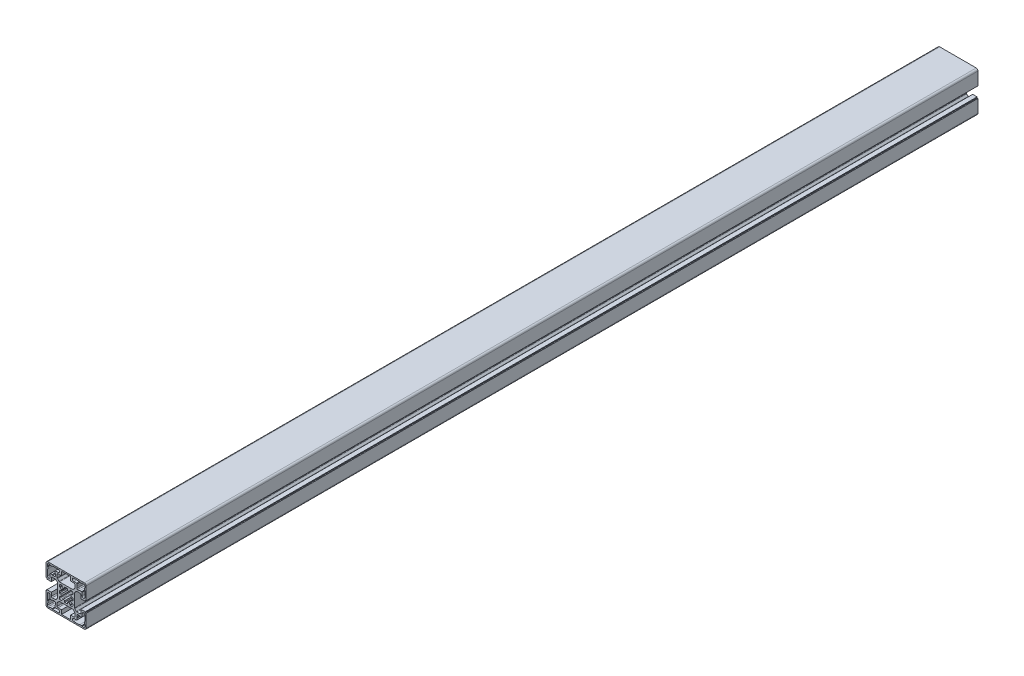
SolidWorks part; units mm, degrees
ref_plane "前视基准面" through (0, 0, 0) normal (0, 0, 1) x (1, 0, 0)
ref_plane "上视基准面" through (0, 0, 0) normal (0, 1, 0) x (1, 0, 0)
ref_plane "右视基准面" through (0, 0, 0) normal (1, 0, 0) x (0, 0, -1)
sketch "草图1" plane through (0, 0, 0) normal (0, 0, 1) x (1, 0, 0)
  line L8 (30.535, 44.0271) -> (29.0823, 45.4798)
  line L9 (31.4137, 44.0271) -> (30.535, 44.0271)
  line L10 (31.4137, 42.0271) -> (31.4137, 44.0271)
  line L11 (28.4137, 41.0271) -> (30.4137, 41.0271)
  line L12 (28.4137, 41.9058) -> (28.4137, 41.0271)
  line L13 (26.961, 43.3585) -> (28.4137, 41.9058)
  line L14 (25.4137, 41.0271) -> (25.4137, 42.7176)
  line L15 (22.4137, 41.0271) -> (25.4137, 41.0271)
  line L16 (22.4137, 42.7176) -> (22.4137, 41.0271)
  line L17 (19.4137, 41.9058) -> (20.8664, 43.3585)
  line L18 (19.4137, 41.0271) -> (19.4137, 41.9058)
  line L19 (17.4137, 41.0271) -> (19.4137, 41.0271)
  line L20 (16.4137, 44.0271) -> (16.4137, 42.0271)
  line L21 (17.2924, 44.0271) -> (16.4137, 44.0271)
  line L22 (18.7451, 45.4798) -> (17.2924, 44.0271)
  line L23 (16.4137, 47.0271) -> (18.1042, 47.0271)
  line L24 (16.4137, 50.0271) -> (16.4137, 47.0271)
  line L25 (18.1042, 50.0271) -> (16.4137, 50.0271)
  line L26 (17.2924, 53.0271) -> (18.7451, 51.5744)
  line L27 (16.4137, 53.0271) -> (17.2924, 53.0271)
  line L28 (16.4137, 55.0271) -> (16.4137, 53.0271)
  line L29 (19.4137, 56.0271) -> (17.4137, 56.0271)
  line L30 (19.4137, 55.1484) -> (19.4137, 56.0271)
  line L31 (20.8664, 53.6957) -> (19.4137, 55.1484)
  line L32 (22.4137, 56.0271) -> (22.4137, 54.3366)
  line L33 (25.4137, 56.0271) -> (22.4137, 56.0271)
  line L34 (25.4137, 54.3366) -> (25.4137, 56.0271)
  line L35 (28.4137, 55.1484) -> (26.961, 53.6957)
  line L36 (28.4137, 56.0271) -> (28.4137, 55.1484)
  line L37 (30.4137, 56.0271) -> (28.4137, 56.0271)
  line L38 (31.4137, 53.0271) -> (31.4137, 55.0271)
  line L39 (30.535, 53.0271) -> (31.4137, 53.0271)
  line L40 (29.0823, 51.5744) -> (30.535, 53.0271)
  line L41 (31.4137, 50.0271) -> (29.7232, 50.0271)
  line L42 (31.4137, 47.0271) -> (31.4137, 50.0271)
  line L43 (29.7232, 47.0271) -> (31.4137, 47.0271)
  line L44 (11.4137, 66.0271) -> (11.9137, 66.5271)
  line L45 (11.4137, 64.0271) -> (11.4137, 66.0271)
  line L46 (11.9137, 63.5271) -> (11.4137, 64.0271)
  line L47 (11.9137, 61.5271) -> (11.9137, 63.5271)
  line L48 (8.9137, 60.5271) -> (10.9137, 60.5271)
  line L49 (8.4137, 61.0271) -> (8.9137, 60.5271)
  line L50 (6.4137, 61.0271) -> (8.4137, 61.0271)
  line L51 (5.9137, 60.5271) -> (6.4137, 61.0271)
  line L52 (5.9137, 57.1271) -> (5.9137, 60.5271)
  line L53 (2.9137, 63.5271) -> (2.9137, 57.1271)
  line L54 (3.4137, 64.0271) -> (2.9137, 63.5271)
  line L55 (3.4137, 66.0271) -> (3.4137, 64.0271)
  line L56 (2.9137, 66.5271) -> (3.4137, 66.0271)
  line L57 (2.9137, 68.5271) -> (2.9137, 66.5271)
  line L58 (5.9137, 69.5271) -> (3.9137, 69.5271)
  line L59 (6.4137, 69.0271) -> (5.9137, 69.5271)
  line L60 (8.4137, 69.0271) -> (6.4137, 69.0271)
  line L61 (8.9137, 69.5271) -> (8.4137, 69.0271)
  line L62 (15.3137, 69.5271) -> (8.9137, 69.5271)
  line L63 (11.9137, 66.5271) -> (15.3137, 66.5271)
  line L64 (15.3137, 30.5271) -> (11.9137, 30.5271)
  line L65 (8.9137, 27.5271) -> (15.3137, 27.5271)
  line L66 (8.4137, 28.0271) -> (8.9137, 27.5271)
  line L67 (6.4137, 28.0271) -> (8.4137, 28.0271)
  line L68 (5.9137, 27.5271) -> (6.4137, 28.0271)
  line L69 (3.9137, 27.5271) -> (5.9137, 27.5271)
  line L70 (2.9137, 30.5271) -> (2.9137, 28.5271)
  line L71 (3.4137, 31.0271) -> (2.9137, 30.5271)
  line L72 (3.4137, 33.0271) -> (3.4137, 31.0271)
  line L73 (2.9137, 33.5271) -> (3.4137, 33.0271)
  line L74 (2.9137, 39.9271) -> (2.9137, 33.5271)
  line L75 (5.9137, 36.5271) -> (5.9137, 39.9271)
  line L76 (6.4137, 36.0271) -> (5.9137, 36.5271)
  line L77 (8.4137, 36.0271) -> (6.4137, 36.0271)
  line L78 (8.9137, 36.5271) -> (8.4137, 36.0271)
  line L79 (10.9137, 36.5271) -> (8.9137, 36.5271)
  line L80 (11.9137, 33.5271) -> (11.9137, 35.5271)
  line L81 (11.4137, 33.0271) -> (11.9137, 33.5271)
  line L82 (11.4137, 31.0271) -> (11.4137, 33.0271)
  line L83 (11.9137, 30.5271) -> (11.4137, 31.0271)
  line L84 (41.9137, 39.9271) -> (41.9137, 36.5271)
  line L85 (44.9137, 33.5271) -> (44.9137, 39.9271)
  line L86 (44.4137, 33.0271) -> (44.9137, 33.5271)
  line L87 (44.4137, 31.0271) -> (44.4137, 33.0271)
  line L88 (44.9137, 30.5271) -> (44.4137, 31.0271)
  line L89 (44.9137, 28.5271) -> (44.9137, 30.5271)
  line L90 (41.9137, 27.5271) -> (43.9137, 27.5271)
  line L91 (41.4137, 28.0271) -> (41.9137, 27.5271)
  line L92 (39.4137, 28.0271) -> (41.4137, 28.0271)
  line L93 (38.9137, 27.5271) -> (39.4137, 28.0271)
  line L94 (32.5137, 27.5271) -> (38.9137, 27.5271)
  line L95 (35.9137, 30.5271) -> (32.5137, 30.5271)
  line L96 (36.4137, 31.0271) -> (35.9137, 30.5271)
  line L97 (36.4137, 33.0271) -> (36.4137, 31.0271)
  line L98 (35.9137, 33.5271) -> (36.4137, 33.0271)
  line L99 (35.9137, 35.5271) -> (35.9137, 33.5271)
  line L100 (38.9137, 36.5271) -> (36.9137, 36.5271)
  line L101 (39.4137, 36.0271) -> (38.9137, 36.5271)
  line L102 (41.4137, 36.0271) -> (39.4137, 36.0271)
  line L103 (41.9137, 36.5271) -> (41.4137, 36.0271)
  line L104 (32.5137, 66.5271) -> (35.9137, 66.5271)
  line L105 (38.9137, 69.5271) -> (32.5137, 69.5271)
  line L106 (39.4137, 69.0271) -> (38.9137, 69.5271)
  line L107 (41.4137, 69.0271) -> (39.4137, 69.0271)
  line L108 (41.9137, 69.5271) -> (41.4137, 69.0271)
  line L109 (43.9137, 69.5271) -> (41.9137, 69.5271)
  line L110 (44.9137, 66.5271) -> (44.9137, 68.5271)
  line L111 (44.4137, 66.0271) -> (44.9137, 66.5271)
  line L112 (44.4137, 64.0271) -> (44.4137, 66.0271)
  line L113 (44.9137, 63.5271) -> (44.4137, 64.0271)
  line L114 (44.9137, 57.1271) -> (44.9137, 63.5271)
  line L115 (41.9137, 60.5271) -> (41.9137, 57.1271)
  line L116 (41.4137, 61.0271) -> (41.9137, 60.5271)
  line L117 (39.4137, 61.0271) -> (41.4137, 61.0271)
  line L118 (38.9137, 60.5271) -> (39.4137, 61.0271)
  line L119 (36.9137, 60.5271) -> (38.9137, 60.5271)
  line L120 (35.9137, 63.5271) -> (35.9137, 61.5271)
  line L121 (36.4137, 64.0271) -> (35.9137, 63.5271)
  line L122 (36.4137, 66.0271) -> (36.4137, 64.0271)
  line L123 (35.9137, 66.5271) -> (36.4137, 66.0271)
  line L124 (29.0137, 69.5271) -> (18.8137, 69.5271)
  line L125 (29.0137, 65.0271) -> (29.0137, 69.5271)
  line L126 (32.9137, 65.0271) -> (29.0137, 65.0271)
  line L127 (33.9137, 60.7091) -> (33.9137, 64.0271)
  line L128 (31.9388, 58.32) -> (33.6208, 60.002)
  line L129 (16.5957, 58.0271) -> (31.2317, 58.0271)
  line L130 (14.2066, 60.002) -> (15.8886, 58.32)
  line L131 (13.9137, 64.0271) -> (13.9137, 60.7091)
  line L132 (18.8137, 65.0271) -> (14.9137, 65.0271)
  line L133 (18.8137, 69.5271) -> (18.8137, 65.0271)
  line L134 (29.0137, 32.0271) -> (32.9137, 32.0271)
  line L135 (29.0137, 27.5271) -> (29.0137, 32.0271)
  line L136 (18.8137, 27.5271) -> (29.0137, 27.5271)
  line L137 (18.8137, 32.0271) -> (18.8137, 27.5271)
  line L138 (14.9137, 32.0271) -> (18.8137, 32.0271)
  line L139 (13.9137, 36.3451) -> (13.9137, 33.0271)
  line L140 (15.8886, 38.7342) -> (14.2066, 37.0522)
  line L141 (31.2317, 39.0271) -> (16.5957, 39.0271)
  line L142 (33.6208, 37.0522) -> (31.9388, 38.7342)
  line L143 (33.9137, 33.0271) -> (33.9137, 36.3451)
  line L144 (46.4137, 42.4271) -> (46.4137, 28.0271)
  line L145 (45.4137, 42.4271) -> (46.4137, 42.4271)
  line L146 (45.4137, 43.4271) -> (45.4137, 42.4271)
  line L147 (40.4137, 43.4271) -> (45.4137, 43.4271)
  line L148 (40.4137, 39.5271) -> (40.4137, 43.4271)
  line L149 (36.0957, 38.5271) -> (39.4137, 38.5271)
  line L150 (33.7066, 40.502) -> (35.3886, 38.82)
  line L151 (33.4137, 55.8451) -> (33.4137, 41.2091)
  line L152 (35.3886, 58.2342) -> (33.7066, 56.5522)
  line L153 (39.4137, 58.5271) -> (36.0957, 58.5271)
  line L154 (40.4137, 53.6271) -> (40.4137, 57.5271)
  line L155 (45.4137, 53.6271) -> (40.4137, 53.6271)
  line L156 (45.4137, 54.6271) -> (45.4137, 53.6271)
  line L157 (46.4137, 54.6271) -> (45.4137, 54.6271)
  line L158 (46.4137, 69.0271) -> (46.4137, 54.6271)
  line L159 (3.4137, 71.0271) -> (44.4137, 71.0271)
  line L160 (1.4137, 54.6271) -> (1.4137, 69.0271)
  line L161 (2.4137, 54.6271) -> (1.4137, 54.6271)
  line L162 (2.4137, 53.6271) -> (2.4137, 54.6271)
  line L163 (7.4137, 53.6271) -> (2.4137, 53.6271)
  line L164 (7.4137, 57.5271) -> (7.4137, 53.6271)
  line L165 (11.7317, 58.5271) -> (8.4137, 58.5271)
  line L166 (14.1208, 56.5522) -> (12.4388, 58.2342)
  line L167 (14.4137, 41.2091) -> (14.4137, 55.8451)
  line L168 (12.4388, 38.82) -> (14.1208, 40.502)
  line L169 (8.4137, 38.5271) -> (11.7317, 38.5271)
  line L170 (7.4137, 43.4271) -> (7.4137, 39.5271)
  line L171 (2.4137, 43.4271) -> (7.4137, 43.4271)
  line L172 (2.4137, 42.4271) -> (2.4137, 43.4271)
  line L173 (1.4137, 42.4271) -> (2.4137, 42.4271)
  line L174 (1.4137, 28.0271) -> (1.4137, 42.4271)
  line L175 (44.4137, 26.0271) -> (3.4137, 26.0271)
  arc A0 (30.4137, 41.0271) -> (31.4137, 42.0271) centre (30.4137, 42.0271) ccw
  arc A1 (25.4137, 42.7176) -> (26.961, 43.3585) centre (23.9137, 48.5271) ccw
  arc A2 (20.8664, 43.3585) -> (22.4137, 42.7176) centre (23.9137, 48.5271) ccw
  arc A3 (16.4137, 42.0271) -> (17.4137, 41.0271) centre (17.4137, 42.0271) ccw
  arc A4 (18.1042, 47.0271) -> (18.7451, 45.4798) centre (23.9137, 48.5271) ccw
  arc A5 (18.7451, 51.5744) -> (18.1042, 50.0271) centre (23.9137, 48.5271) ccw
  arc A6 (17.4137, 56.0271) -> (16.4137, 55.0271) centre (17.4137, 55.0271) ccw
  arc A7 (22.4137, 54.3366) -> (20.8664, 53.6957) centre (23.9137, 48.5271) ccw
  arc A8 (26.961, 53.6957) -> (25.4137, 54.3366) centre (23.9137, 48.5271) ccw
  arc A9 (31.4137, 55.0271) -> (30.4137, 56.0271) centre (30.4137, 55.0271) ccw
  arc A10 (29.7232, 50.0271) -> (29.0823, 51.5744) centre (23.9137, 48.5271) ccw
  arc A11 (29.0823, 45.4798) -> (29.7232, 47.0271) centre (23.9137, 48.5271) ccw
  arc A12 (10.9137, 60.5271) -> (11.9137, 61.5271) centre (10.9137, 61.5271) ccw
  arc A13 (2.9137, 57.1271) -> (5.9137, 57.1271) centre (4.4137, 57.1271) ccw
  arc A14 (3.9137, 69.5271) -> (2.9137, 68.5271) centre (3.9137, 68.5271) ccw
  arc A15 (15.3137, 66.5271) -> (15.3137, 69.5271) centre (15.3137, 68.0271) ccw
  arc A16 (15.3137, 27.5271) -> (15.3137, 30.5271) centre (15.3137, 29.0271) ccw
  arc A17 (2.9137, 28.5271) -> (3.9137, 27.5271) centre (3.9137, 28.5271) ccw
  arc A18 (5.9137, 39.9271) -> (2.9137, 39.9271) centre (4.4137, 39.9271) ccw
  arc A19 (11.9137, 35.5271) -> (10.9137, 36.5271) centre (10.9137, 35.5271) ccw
  arc A20 (44.9137, 39.9271) -> (41.9137, 39.9271) centre (43.4137, 39.9271) ccw
  arc A21 (43.9137, 27.5271) -> (44.9137, 28.5271) centre (43.9137, 28.5271) ccw
  arc A22 (32.5137, 30.5271) -> (32.5137, 27.5271) centre (32.5137, 29.0271) ccw
  arc A23 (36.9137, 36.5271) -> (35.9137, 35.5271) centre (36.9137, 35.5271) ccw
  arc A24 (32.5137, 69.5271) -> (32.5137, 66.5271) centre (32.5137, 68.0271) ccw
  arc A25 (44.9137, 68.5271) -> (43.9137, 69.5271) centre (43.9137, 68.5271) ccw
  arc A26 (41.9137, 57.1271) -> (44.9137, 57.1271) centre (43.4137, 57.1271) ccw
  arc A27 (35.9137, 61.5271) -> (36.9137, 60.5271) centre (36.9137, 61.5271) ccw
  arc A28 (33.9137, 64.0271) -> (32.9137, 65.0271) centre (32.9137, 64.0271) ccw
  arc A29 (33.6208, 60.002) -> (33.9137, 60.7091) centre (32.9137, 60.7091) ccw
  arc A30 (31.2317, 58.0271) -> (31.9388, 58.32) centre (31.2317, 59.0271) ccw
  arc A31 (15.8886, 58.32) -> (16.5957, 58.0271) centre (16.5957, 59.0271) ccw
  arc A32 (13.9137, 60.7091) -> (14.2066, 60.002) centre (14.9137, 60.7091) ccw
  arc A33 (14.9137, 65.0271) -> (13.9137, 64.0271) centre (14.9137, 64.0271) ccw
  arc A34 (13.9137, 33.0271) -> (14.9137, 32.0271) centre (14.9137, 33.0271) ccw
  arc A35 (14.2066, 37.0522) -> (13.9137, 36.3451) centre (14.9137, 36.3451) ccw
  arc A36 (16.5957, 39.0271) -> (15.8886, 38.7342) centre (16.5957, 38.0271) ccw
  arc A37 (31.9388, 38.7342) -> (31.2317, 39.0271) centre (31.2317, 38.0271) ccw
  arc A38 (33.9137, 36.3451) -> (33.6208, 37.0522) centre (32.9137, 36.3451) ccw
  arc A39 (32.9137, 32.0271) -> (33.9137, 33.0271) centre (32.9137, 33.0271) ccw
  arc A40 (44.4137, 26.0271) -> (46.4137, 28.0271) centre (44.4137, 28.0271) ccw
  arc A41 (39.4137, 38.5271) -> (40.4137, 39.5271) centre (39.4137, 39.5271) ccw
  arc A42 (35.3886, 38.82) -> (36.0957, 38.5271) centre (36.0957, 39.5271) ccw
  arc A43 (33.4137, 41.2091) -> (33.7066, 40.502) centre (34.4137, 41.2091) ccw
  arc A44 (33.7066, 56.5522) -> (33.4137, 55.8451) centre (34.4137, 55.8451) ccw
  arc A45 (36.0957, 58.5271) -> (35.3886, 58.2342) centre (36.0957, 57.5271) ccw
  arc A46 (40.4137, 57.5271) -> (39.4137, 58.5271) centre (39.4137, 57.5271) ccw
  arc A47 (46.4137, 69.0271) -> (44.4137, 71.0271) centre (44.4137, 69.0271) ccw
  arc A48 (3.4137, 71.0271) -> (1.4137, 69.0271) centre (3.4137, 69.0271) ccw
  arc A49 (8.4137, 58.5271) -> (7.4137, 57.5271) centre (8.4137, 57.5271) ccw
  arc A50 (12.4388, 58.2342) -> (11.7317, 58.5271) centre (11.7317, 57.5271) ccw
  arc A51 (14.4137, 55.8451) -> (14.1208, 56.5522) centre (13.4137, 55.8451) ccw
  arc A52 (14.1208, 40.502) -> (14.4137, 41.2091) centre (13.4137, 41.2091) ccw
  arc A53 (11.7317, 38.5271) -> (12.4388, 38.82) centre (11.7317, 39.5271) ccw
  arc A54 (7.4137, 39.5271) -> (8.4137, 38.5271) centre (8.4137, 39.5271) ccw
  arc A55 (1.4137, 28.0271) -> (3.4137, 26.0271) centre (3.4137, 28.0271) ccw
extrude "拉伸1" add sketch "草图1" along normal blind 1000
